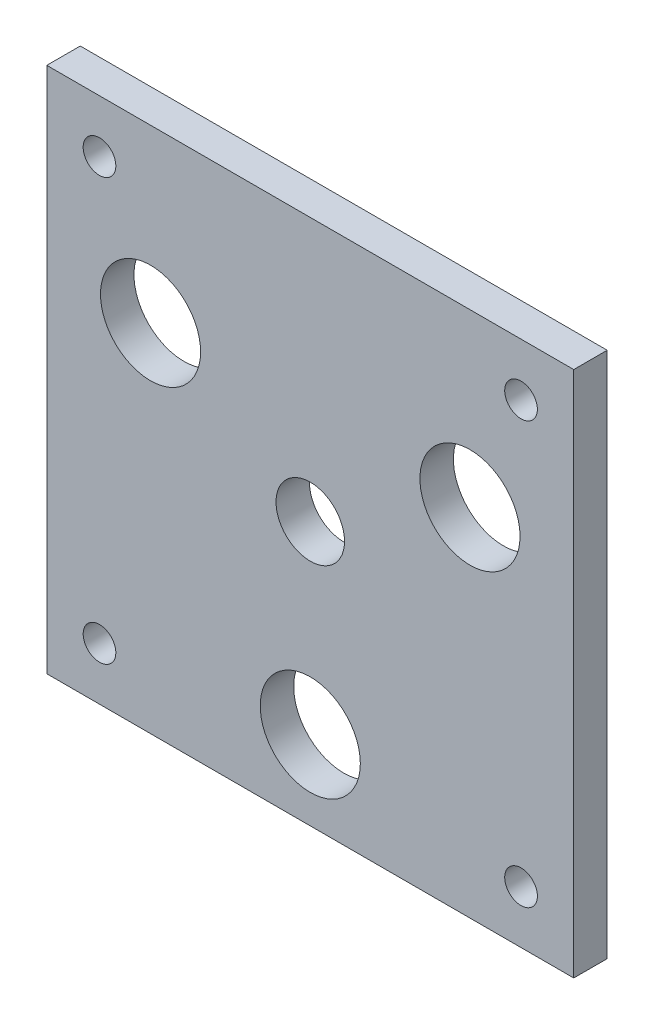
SolidWorks part; units mm, degrees
ref_plane "Alzado" through (0, 0, 0) normal (0, 0, 1) x (1, 0, 0)
ref_plane "Planta" through (0, 0, 0) normal (0, 1, 0) x (1, 0, 0)
ref_plane "Vista lateral" through (0, 0, 0) normal (1, 0, 0) x (0, 0, -1)
sketch "Croquis1" plane through (0, 0, 0) normal (0, 0, 1) x (1, 0, 0)
  line L0 (0, -35) -> (30.3109, 17.5) construction
  line L1 (-50, -50) -> (50, -50)
  line L2 (-50, -50) -> (-50, 50)
  line L3 (-50, 50) -> (50, 50)
  line L4 (50, -50) -> (50, 50)
  line L5 (-50, -50) -> (50, 50) construction
  line L6 (-50, 50) -> (50, -50) construction
  line L7 (30.3109, 17.5) -> (-30.3109, 17.5) construction
  line L8 (-30.3109, 17.5) -> (0, -35) construction
  line L9 (0, -35) -> (0, 0) construction
  circle A1 centre (0, -35) radius 9.5
  circle A2 centre (-30.3109, 17.5) radius 9.5
  circle A3 centre (30.3109, 17.5) radius 9.5
  point P0 (0, 0)
  point P17 (0, 0)
  dimension "D3" = 35
  dimension "D4" = 19
  dimension "D1" = 100
  dimension "D2" = 100
  dimension "D6" = 60.6218
  dimension "D5" = 3
extrude "Saliente-Extruir1" add sketch "Croquis1" along normal blind 6.35
sketch "Croquis2" plane through (0, 0, 6.35) normal (0, 0, 1) x (1, 0, 0)
  line L0 (-40, 40) -> (40, 40) construction
  line L1 (40, 40) -> (40, -40) construction
  line L2 (40, -40) -> (-40, -40) construction
  line L3 (-40, -40) -> (-40, 40) construction
  line L4 (-50, 50) -> (-50, -50) construction
  line L5 (-50, -50) -> (50, -50) construction
  circle A0 centre (0, 0) radius 6.5
  circle A1 centre (-40, 40) radius 3.1
  circle A2 centre (40, 40) radius 3.1
  circle A3 centre (-40, -40) radius 3.1
  circle A4 centre (40, -40) radius 3.1
  dimension "D1" = 13
  dimension "D2" = 6.2
  dimension "D3" = 6.2
  dimension "D4" = 6.2
  dimension "D5" = 6.2
  dimension "D6" = 80
  dimension "D7" = 80
  dimension "D8" = 10
  dimension "D9" = 10
extrude "Cortar-Extruir1" cut sketch "Croquis2" against normal up to next
